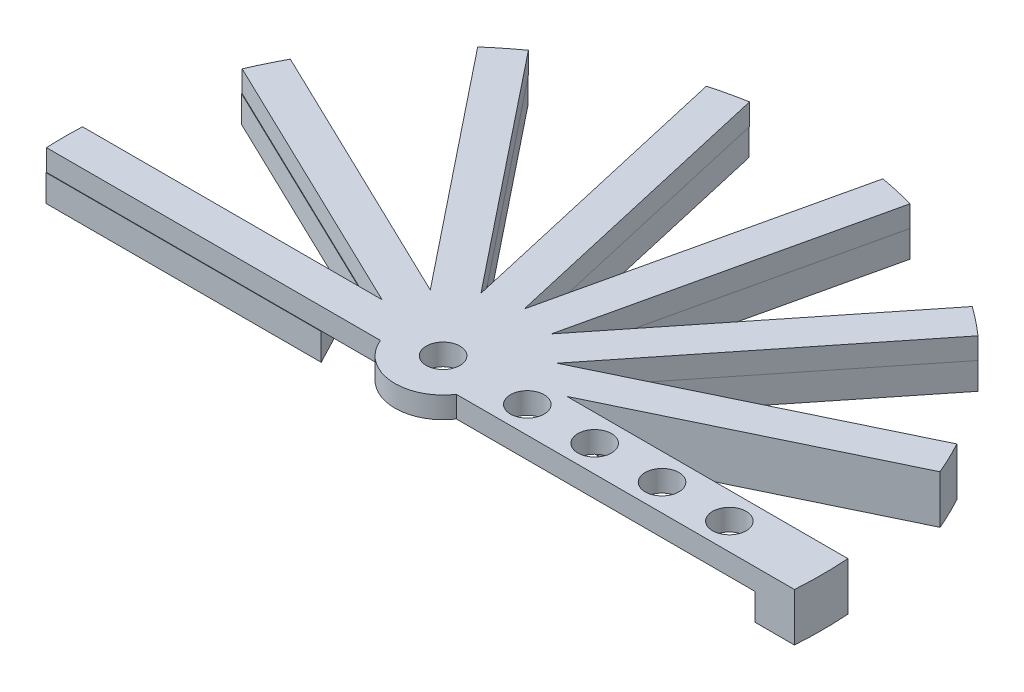
SolidWorks part; units mm, degrees
ref_plane "Front Plane" through (0, 0, 0) normal (0, 0, 1) x (1, 0, 0)
ref_plane "Top Plane" through (0, 0, 0) normal (0, 1, 0) x (1, 0, 0)
ref_plane "Right Plane" through (0, 0, 0) normal (1, 0, 0) x (0, 0, -1)
sketch "Sketch1" plane through (0, 0, 0) normal (0, 1, 0) x (1, 0, 0)
  line L0 (3.9267, 0.0281) -> (-4.0733, 0.0281) construction
  line L1 (31.9267, 0.0281) -> (44.8807, 0.0281)
  line L2 (44.8807, 3.2031) -> (44.8807, -3.1469)
  line L3 (44.8807, -3.1469) -> (0, -3.1469)
  line L4 (0, -3.1469) -> (0, 3.2031)
  line L5 (0, 3.2031) -> (44.8807, 3.2031)
  line L26 (0, 3.1469) -> (0, -3.2031)
  line L42 (44.8807, 2.171) -> (44.8807, -2.1147)
  line L43 (29.5103, -33.9606) -> (-2.2252, -2.2252) [skipped]
  line L44 (34.0004, -29.4705) -> (29.5103, -33.9606) [skipped]
  line L45 (2.2649, 2.2649) -> (34.0004, -29.4705) [skipped]
  line L46 (44.8807, -2.1147) -> (0, -2.1147)
  line L47 (-3.1469, -44.8807) -> (-3.1469, 0) [skipped]
  line L48 (3.2031, -44.8807) -> (-3.1469, -44.8807) [skipped]
  line L49 (3.2031, 0) -> (3.2031, -44.8807) [skipped]
  line L50 (0, -2.1147) -> (0, 2.171)
  line L51 (-33.9606, -29.5103) -> (-2.2252, 2.2252) [skipped]
  line L52 (-29.4705, -34.0004) -> (-33.9606, -29.5103) [skipped]
  line L53 (2.2649, -2.2649) -> (-29.4705, -34.0004) [skipped]
  line L54 (0, 2.171) -> (44.8807, 2.171)
  line L55 (-44.8807, -3.2031) -> (-44.8807, 3.1469) [skipped]
  line L56 (-1.3331, 3.7261) -> (39.103, 23.1991)
  line L57 (-34.0004, 29.4705) -> (-29.5103, 33.9606) [skipped]
  line L58 (-44.8807, 3.1469) -> (0, 3.1469) [skipped]
  line L59 (0, -3.2031) -> (-44.8807, -3.2031) [skipped]
  line L60 (-29.5103, 33.9606) -> (2.2252, 2.2252) [skipped]
  line L61 (-2.2649, -2.2649) -> (-34.0004, 29.4705) [skipped]
  line L62 (39.103, 23.1991) -> (40.9625, 19.3378)
  line L63 (3.1469, 44.8807) -> (3.1469, 0) [skipped]
  line L64 (-3.2031, 44.8807) -> (3.1469, 44.8807) [skipped]
  line L65 (-3.2031, 0) -> (-3.2031, 44.8807) [skipped]
  line L66 (40.9625, 19.3378) -> (0.5264, -0.1352)
  line L67 (33.9606, 29.5103) -> (2.2252, -2.2252) [skipped]
  line L68 (-2.2649, 2.2649) -> (29.4705, 34.0004) [skipped]
  line L69 (29.4705, 34.0004) -> (33.9606, 29.5103) [skipped]
  line L70 (-3.1469, 0) -> (3.2031, 0) [skipped]
  line L71 (-2.2252, -2.2252) -> (2.2649, 2.2649) [skipped]
  line L72 (-2.2252, 2.2252) -> (2.2649, -2.2649) [skipped]
  line L73 (2.2252, 2.2252) -> (-2.2649, -2.2649) [skipped]
  line L74 (3.1469, 0) -> (-3.2031, 0) [skipped]
  line L75 (2.2252, -2.2252) -> (-2.2649, 2.2649) [skipped]
  line L76 (0.5264, -0.1352) -> (-1.3331, 3.7261)
  line L77 (-3.209, 4.5488) -> (24.7737, 39.6379)
  line L78 (24.7737, 39.6379) -> (28.1244, 36.9658)
  line L79 (28.1244, 36.9658) -> (0.1417, 1.8767)
  line L80 (0.1417, 1.8767) -> (-3.209, 4.5488)
  line L81 (-5.256, 4.4761) -> (4.7309, 48.2316)
  line L82 (4.7309, 48.2316) -> (8.9091, 47.2779)
  line L83 (8.9091, 47.2779) -> (-1.0778, 3.5224)
  line L84 (-1.0778, 3.5224) -> (-5.256, 4.4761)
  line L85 (-7.0688, 3.5224) -> (-17.0557, 47.2779)
  line L86 (-17.0557, 47.2779) -> (-12.8775, 48.2316)
  line L87 (-12.8775, 48.2316) -> (-2.8906, 4.4761)
  line L88 (-2.8906, 4.4761) -> (-7.0688, 3.5224)
  line L89 (-8.2883, 1.8767) -> (-36.271, 36.9658)
  line L90 (-36.271, 36.9658) -> (-32.9203, 39.6379)
  line L91 (-32.9203, 39.6379) -> (-4.9376, 4.5488)
  line L92 (-4.9376, 4.5488) -> (-8.2883, 1.8767)
  line L93 (-8.6729, -0.1352) -> (-49.1091, 19.3378)
  line L94 (-49.1091, 19.3378) -> (-47.2496, 23.1991)
  line L95 (-47.2496, 23.1991) -> (-6.8134, 3.7261)
  line L96 (-6.8134, 3.7261) -> (-8.6729, -0.1352)
  line L97 (-8.1466, -2.1147) -> (-53.0273, -2.1147)
  line L98 (-53.0273, -2.1147) -> (-53.0273, 2.171)
  line L99 (-53.0273, 2.171) -> (-8.1466, 2.171)
  line L100 (-8.1466, 2.171) -> (-8.1466, -2.1147)
  circle A4 centre (5.9267, 0.0281) radius 2
  circle A5 centre (13.9267, 0.0281) radius 2
  circle A6 centre (21.9267, 0.0281) radius 2
  circle A7 centre (29.9267, 0.0281) radius 2
  circle A9 centre (-4.0733, 0.0281) radius 5.7156
  circle A14 centre (-4.0733, 0.0281) radius 2
  point P5 (44.8807, 0.0281)
  point P22 (44.8807, 0.0281)
  point P25 (0, 0.0281)
  point P51 (-4.0733, 0.0281)
  point P59 (-4.0733, 0.0281)
  point P64 (0, 0)
  point P119 (0, 0)
  dimension "D2" = 8
  dimension "D5" = 4
  dimension "D1" = 8
  dimension "D6" = 12.954
  dimension "D7" = 6.35
extrude "Boss-Extrude1" add sketch "Sketch1" along normal blind 2.54
sketch "Sketch3" plane through (0, 0, 0) normal (0, -1, 0) x (1, 0, 0)
  line L0 (40.9625, -19.3378) -> (39.103, -23.1991)
  line L1 (39.103, -23.1991) -> (6.046, -7.2797)
  line L2 (3.4557, -6.0322) -> (39.103, -23.1991) construction
  line L3 (6.046, -7.2797) -> (9.9322, -4.3944)
  line L4 (40.9625, -19.3378) -> (7.4584, -3.2031) construction
  line L5 (9.9322, -4.3944) -> (40.9625, -19.3378)
  line L6 (6.6384, -10.0361) -> (28.1117, -36.9635)
  line L7 (24.761, -39.6355) -> (1.8852, -10.9494)
  line L8 (28.1117, -36.9635) -> (24.761, -39.6355)
  line L9 (1.8852, -10.9494) -> (6.6384, -10.0361)
  line L10 (1.2229, -13.6899) -> (8.886, -47.2676)
  line L11 (4.7077, -48.2212) -> (-3.4558, -12.4504)
  line L12 (8.886, -47.2676) -> (4.7077, -48.2212)
  line L13 (-3.4558, -12.4504) -> (1.2229, -13.6899)
  line L14 (-5.2415, -14.6321) -> (-12.9067, -48.2094)
  line L15 (-17.0849, -47.2556) -> (-8.9191, -11.4853)
  line L16 (-12.9067, -48.2094) -> (-17.0849, -47.2556)
  line L17 (-8.9191, -11.4853) -> (-5.2415, -14.6321)
  line L18 (-11.4746, -12.6761) -> (-32.9496, -39.6021)
  line L19 (-36.3002, -36.9299) -> (-13.4226, -8.2452)
  line L20 (-32.9496, -39.6021) -> (-36.3002, -36.9299)
  line L21 (-13.4226, -8.2452) -> (-11.4746, -12.6761)
  line L22 (-16.2417, -8.2093) -> (-47.273, -23.1508)
  line L23 (-49.1322, -19.2894) -> (-16.0743, -3.372)
  line L24 (-47.273, -23.1508) -> (-49.1322, -19.2894)
  line L25 (-16.0743, -3.372) -> (-16.2417, -8.2093)
  line L26 (-18.5986, -2.1164) -> (-53.0396, -2.1139)
  line L27 (-53.0393, 2.1718) -> (-16.3488, 2.1691)
  line L28 (-53.0396, -2.1139) -> (-53.0393, 2.1718)
  line L29 (-16.3488, 2.1691) -> (-18.5986, -2.1164)
  point P37 (-4.0733, 0)
  dimension "D1" = 7
extrude "Boss-Extrude2" add sketch "Sketch3" along normal blind 3.175
sketch "Sketch4" plane through (0, 0, 0) normal (0, -1, 0) x (1, 0, 0)
  line L0 (44.8807, 3.1469) -> (44.8807, -3.2031)
  line L1 (44.8807, -3.2031) -> (36.1256, -3.2031)
  line L2 (7.4584, -3.2031) -> (44.8807, -3.2031) construction
  line L3 (36.1256, -3.2031) -> (36.1256, 3.1469)
  line L4 (44.8807, 3.1469) -> (0.6794, 3.1469) construction
  line L5 (36.1256, 3.1469) -> (44.8807, 3.1469)
extrude "Boss-Extrude3" add sketch "Sketch4" along normal blind 3.175
sketch "Sketch5" plane through (0, 2.54, 0) normal (0, 1, 0) x (1, 0, 0)
  circle A0 centre (-4.0733, 0.0281) radius 56.9524
  circle A1 centre (-4.0733, 0.0281) radius 45.0117
extrude "Cut-Extrude1" cut sketch "Sketch5" against normal blind 15.24
